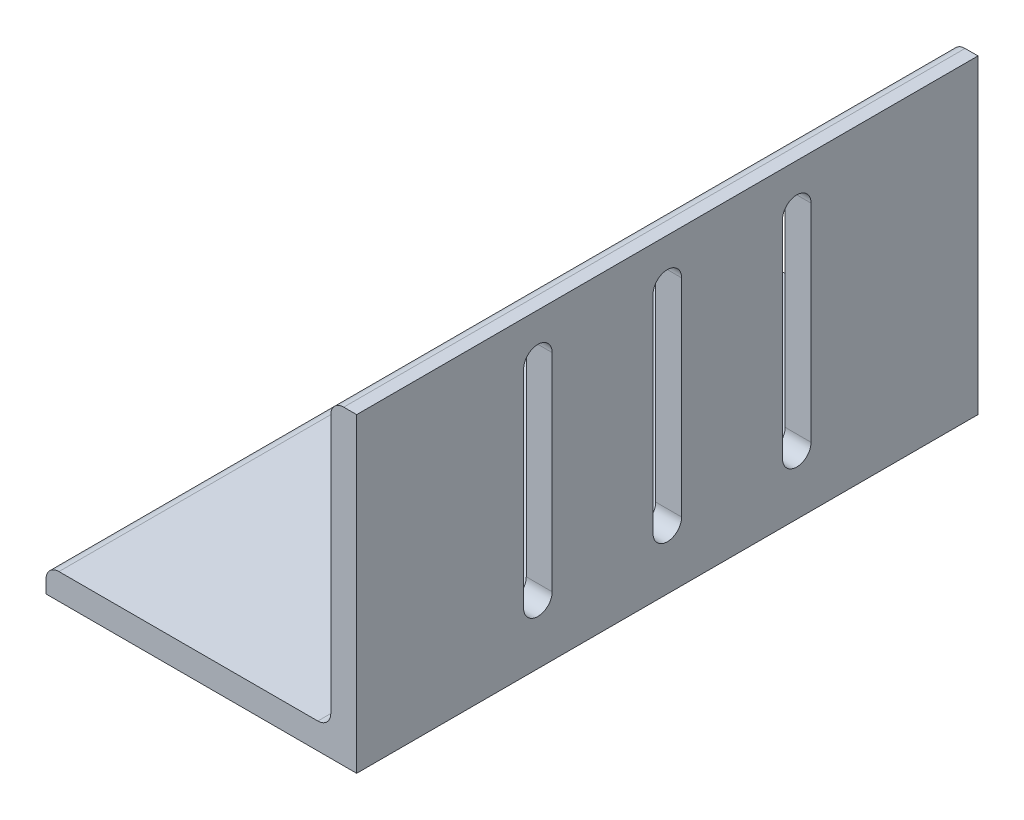
SolidWorks part; units mm, degrees
ref_plane "Front Plane" through (0, 0, 0) normal (0, 0, 1) x (1, 0, 0)
ref_plane "Top Plane" through (0, 0, 0) normal (0, 1, 0) x (1, 0, 0)
ref_plane "Right Plane" through (0, 0, 0) normal (1, 0, 0) x (0, 0, -1)
sketch "Sketch2" plane through (0, 0, 0) normal (0, 0, 1) x (1, 0, 0)
  line L0 (-38.1, 0) -> (38.1, 0)
  line L1 (38.1, 0) -> (38.1, 76.2)
  line L2 (38.1, 76.2) -> (31.75, 76.2) construction
  line L3 (31.75, 73.025) -> (31.75, 9.525)
  line L4 (28.575, 6.35) -> (-34.925, 6.35)
  line L5 (-38.1, 0) -> (-38.1, 6.35) construction
  line L6 (34.925, 76.2) -> (38.1, 76.2)
  line L7 (-38.1, 3.175) -> (-38.1, 0)
  arc A0 (31.75, 73.025) -> (34.925, 76.2) centre (34.925, 73.025) cw
  arc A1 (-38.1, 3.175) -> (-34.925, 6.35) centre (-34.925, 3.175) cw
  arc A2 (31.75, 9.525) -> (28.575, 6.35) centre (28.575, 9.525) cw
  dimension "Vert" = 76.2
  dimension "Horz" = 76.2
  dimension "Thickness" = 6.35
extrude "Boss-Extrude1" add sketch "Sketch2" along normal mid plane 152.4
ref_plane "Contact Plane 1" through (0, 6.35, 0) normal (0, 1, 0) x (1, 0, 0)
ref_plane "Contact Plane 2" through (31.75, 0, 0) normal (-1, 0, 0) x (0, 0, 1)
sketch "Sketch3" plane through (38.1, 0, 0) normal (1, 0, 0) x (0, 0, -1)
  line L0 (-31.75, 65.4) -> (-31.75, 14.6) construction
  line L1 (-28.25, 65.4) -> (-28.25, 14.6)
  line L2 (-35.25, 65.4) -> (-35.25, 14.6)
  line L3 (0, 0) -> (0, 76.2) construction
  line L4 (-76.2, 0) -> (76.2, 0) construction
  line L5 (-76.2, 76.2) -> (76.2, 76.2) construction
  line L6 (31.75, 65.4) -> (31.75, 14.6) construction
  line L7 (28.25, 65.4) -> (28.25, 14.6)
  line L8 (35.25, 65.4) -> (35.25, 14.6)
  line L9 (0, 65.4) -> (0, 14.6) construction
  line L10 (3.5, 65.4) -> (3.5, 14.6)
  line L11 (-3.5, 65.4) -> (-3.5, 14.6)
  arc A0 (-28.25, 65.4) -> (-35.25, 65.4) centre (-31.75, 65.4) ccw
  arc A1 (-35.25, 14.6) -> (-28.25, 14.6) centre (-31.75, 14.6) ccw
  arc A2 (28.25, 65.4) -> (35.25, 65.4) centre (31.75, 65.4) cw
  arc A3 (35.25, 14.6) -> (28.25, 14.6) centre (31.75, 14.6) cw
  arc A4 (3.5, 65.4) -> (-3.5, 65.4) centre (0, 65.4) ccw
  arc A5 (-3.5, 14.6) -> (3.5, 14.6) centre (0, 14.6) ccw
  point P2 (-31.75, 40)
  point P15 (31.75, 40)
  point P22 (0, 40)
  dimension "D1" = 3.5
  dimension "D3" = 31.75
  dimension "D5" = 3.5
  dimension "D2" = 50.8
  dimension "D4" = 40
  dimension "D6" = 50.8
extrude "Cut-Extrude1" cut sketch "Sketch3" against normal blind 10
sketch "Sketch4" plane through (0, 0, 0) normal (0, -1, 0) x (1, 0, 0)
  line L0 (-38.1, 76.2) -> (-38.1, -76.2) construction
  line L1 (-38.1, -76.2) -> (38.1, -76.2) construction
  circle A0 centre (-12.35, 25.4) radius 3.5
  circle A1 centre (-12.35, -25.4) radius 3.5
  circle A2 centre (-12.35, 0) radius 3.5
  point P10 (0, 0)
  dimension "D1" = 7
  dimension "D2" = 7
  dimension "D3" = 25.75
  dimension "D4" = 76.2
extrude "Cut-Extrude2" cut sketch "Sketch4" against normal blind 10
